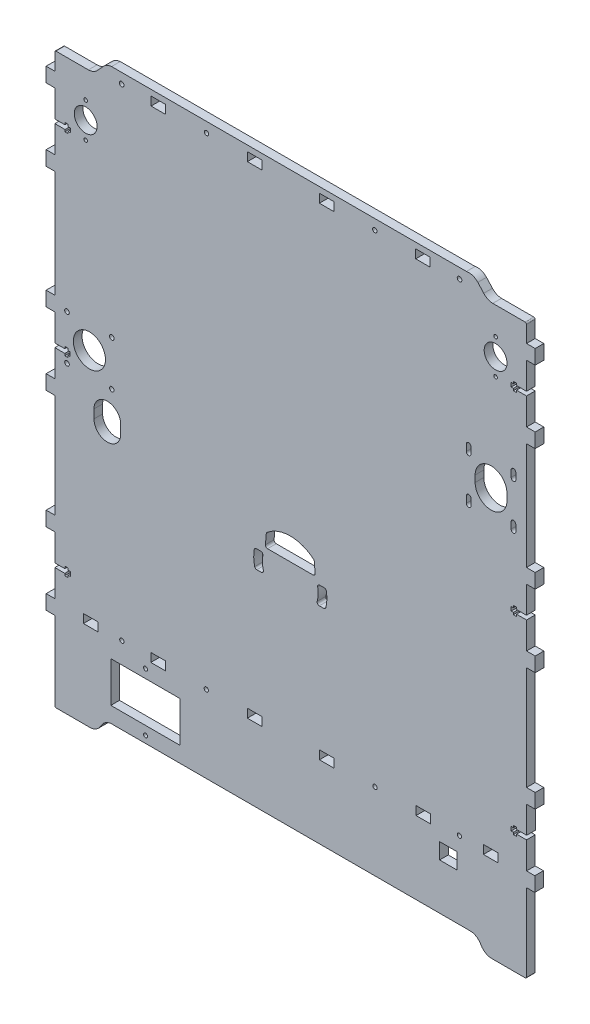
SolidWorks part; units mm, degrees
ref_plane "Спереди" through (0, 0, 0) normal (0, 0, 1) x (1, 0, 0)
ref_plane "Сверху" through (0, 0, 0) normal (0, 1, 0) x (1, 0, 0)
ref_plane "Справа" through (0, 0, 0) normal (1, 0, 0) x (0, 0, -1)
sketch "Эскиз1" plane through (0, 0, 0) normal (0, 0, 1) x (1, 0, 0)
  line L0 (-11.4163, -133.8634) -> (-21.4163, -133.8634)
  line L1 (-21.4163, -133.8634) -> (-21.4163, -127.8634)
  line L2 (-11.4163, -127.8634) -> (-11.4163, -133.8634)
  line L3 (-21.4163, -127.8634) -> (-11.4163, -127.8634)
  line L4 (-61.2563, -127.8634) -> (-61.2563, -133.8634)
  line L5 (-71.2563, -127.8634) -> (-61.2563, -127.8634)
  line L6 (-71.2563, -133.8634) -> (-71.2563, -127.8634)
  line L7 (-61.2563, -133.8634) -> (-71.2563, -133.8634)
  line L8 (61.6637, -152.3271) -> (61.6637, -141.3271)
  line L9 (61.6637, -141.3271) -> (73.7637, -141.3271)
  line L10 (73.7637, -141.3271) -> (73.7637, -152.3271)
  line L11 (73.7637, -152.3271) -> (61.6637, -152.3271)
  line L12 (-197.4876, 21.4243) -> (-197.4866, 20.0542)
  line L13 (-204.4363, 24.2766) -> (-204.4363, 42.8766)
  line L14 (-195.2876, 25.6494) -> (-195.2876, 25.6766)
  line L15 (127.7355, 42.8766) -> (127.7355, 52.8766)
  line L16 (-193.7868, 24.2485) -> (-193.7868, 24.2757)
  line L17 (-195.2868, 24.2757) -> (-195.2876, 25.6494)
  line L18 (-195.2868, 21.4269) -> (-195.2868, 21.4541)
  line L19 (-193.7868, 21.4541) -> (-193.7868, 24.2485)
  line L20 (112.6676, 24.3034) -> (112.6676, 24.2763)
  line L21 (114.8676, 24.3037) -> (114.8674, 25.6766)
  line L22 (-195.2868, 20.0542) -> (-195.2868, 21.4269)
  line L23 (111.1697, 21.5032) -> (111.1697, 21.4761)
  line L24 (111.1676, 24.2752) -> (111.1697, 21.5032)
  line L25 (121.7314, 24.2766) -> (121.7314, 42.8766)
  line L26 (-197.4876, 25.6494) -> (-197.4874, 24.2766)
  line L27 (127.7772, -7.1234) -> (127.7772, 2.8766)
  line L28 (112.6708, 20.1034) -> (112.6708, 20.0763)
  line L29 (-204.4363, 21.4566) -> (-204.4363, 21.4766)
  line L30 (121.7355, 52.8766) -> (121.7355, 127.0366)
  line L31 (-210.4363, 42.8766) -> (-210.4363, 52.8766)
  line L32 (-204.4363, 2.8766) -> (-204.4363, 21.4566)
  line L33 (-204.4363, 52.8766) -> (-204.4363, 127.0366)
  line L34 (-128.0563, -133.8634) -> (-138.0563, -133.8634)
  line L35 (-138.0563, -133.8634) -> (-138.0563, -127.8634)
  line L36 (-138.0563, -127.8634) -> (-128.0563, -127.8634)
  line L37 (-128.0563, -127.8634) -> (-128.0563, -133.8634)
  line L38 (-174.6363, -133.8634) -> (-184.6363, -133.8634)
  line L39 (-184.6363, -133.8634) -> (-184.6363, -127.8634)
  line L40 (-184.6363, -127.8634) -> (-174.6363, -127.8634)
  line L41 (-174.6363, -127.8634) -> (-174.6363, -133.8634)
  line L42 (91.9637, -133.8634) -> (101.9637, -133.8634)
  line L43 (101.9637, -133.8634) -> (101.9637, -127.8634)
  line L44 (101.9637, -127.8634) -> (91.9637, -127.8634)
  line L45 (91.9637, -127.8634) -> (91.9637, -133.8634)
  line L46 (55.3837, -133.8634) -> (45.3837, -133.8634)
  line L47 (45.3837, -133.8634) -> (45.3837, -127.8634)
  line L48 (45.3837, -127.8634) -> (55.3837, -127.8634)
  line L49 (55.3837, -127.8634) -> (55.3837, -133.8634)
  line L50 (-18.1346, -29.194) -> (-21.1843, -29.194)
  line L51 (-21.5365, -41.694) -> (-18.4403, -41.694)
  line L52 (-64.7445, -41.694) -> (-61.6484, -41.694)
  line L53 (-62.0005, -29.194) -> (-65.0502, -29.194)
  line L54 (-58.1883, -16.8245) -> (-58.7957, -23.7669)
  line L55 (-24.3892, -23.7669) -> (-24.9965, -16.8245)
  line L56 (-57.3014, -25.3976) -> (-25.8835, -25.3976)
  line L57 (-165.6924, -145.4128) -> (-165.6924, -173.4128)
  line L58 (-165.6924, -173.4128) -> (-117.6924, -173.4128)
  line L60 (-117.6924, -145.4128) -> (-165.6924, -145.4128)
  line L61 (-181.2137, 199.4366) -> (-203.6703, 199.4366)
  line L62 (-170.8491, 206.6945) -> (-174.9446, 202.2149)
  line L63 (127.478, -128.8434) -> (121.7637, -128.8434)
  line L64 (80.2335, 209.4366) -> (-165.1973, 209.4366)
  line L65 (121.7772, -7.1234) -> (127.7772, -7.1234)
  line L66 (88.0955, 206.8296) -> (92.1957, 202.3542)
  line L67 (98.4674, 199.4366) -> (120.8437, 199.4366)
  line L68 (121.7637, 187.0366) -> (121.7637, 198.5166)
  line L69 (121.7637, 177.0366) -> (127.7637, 177.0366)
  line L70 (127.7637, 177.0366) -> (127.7637, 187.0366)
  line L71 (-204.4363, 42.8766) -> (-210.4363, 42.8766)
  line L72 (120.6695, -193.3271) -> (97.6691, -193.3271)
  line L73 (91.2398, -190.2688) -> (89.1831, -187.2491)
  line L74 (-203.3585, -193.8634) -> (-180.2324, -193.8634)
  line L75 (-210.4363, 177.0366) -> (-210.4363, 187.0366)
  line L76 (114.8517, 158.4366) -> (114.8517, 159.8367)
  line L77 (121.8652, -107.4334) -> (114.8652, -107.4334)
  line L78 (-204.4363, 158.4366) -> (-204.4363, 177.0366)
  line L79 (114.8652, -106.0333) -> (112.6643, -106.0333)
  line L80 (-204.4363, -107.4334) -> (-204.4363, -88.8534)
  line L81 (114.8709, -110.2334) -> (121.7637, -110.2334)
  line L82 (121.8652, -107.4334) -> (121.8652, -88.8534)
  line L83 (111.1668, -110.2331) -> (112.6668, -110.2322)
  line L84 (112.6643, -106.0333) -> (112.6652, -107.4331)
  line L85 (111.1652, -107.434) -> (111.1668, -110.2331)
  line L86 (-197.5237, -111.681) -> (-195.335, -111.6794)
  line L87 (121.7637, 158.4366) -> (114.8517, 158.4366)
  line L88 (114.8708, -111.6332) -> (114.8709, -110.2334)
  line L89 (114.8652, -107.4334) -> (114.8652, -106.0333)
  line L90 (112.6652, -107.4331) -> (111.1652, -107.434)
  line L91 (112.6533, 155.6378) -> (112.6541, 154.2369)
  line L92 (-197.4908, -105.897) -> (-197.4906, -107.4334)
  line L93 (-204.4363, 21.4766) -> (-197.4876, 21.4766)
  line L94 (-197.4876, 21.4766) -> (-197.4876, 21.4243)
  line L95 (-204.4363, 155.6366) -> (-197.3871, 155.6366)
  line L96 (121.7637, -128.8434) -> (121.7637, -110.2334)
  line L97 (121.7801, 2.8766) -> (121.7801, 21.4766)
  line L98 (127.478, -138.8434) -> (127.478, -128.8434)
  line L99 (114.8706, 21.4766) -> (121.7801, 21.4766)
  line L100 (-197.3871, 155.6366) -> (-197.3871, 154.2365)
  line L101 (-197.4181, 158.4366) -> (-204.4363, 158.4366)
  line L102 (-195.2181, 158.419) -> (-195.2181, 159.8366)
  line L103 (112.6668, -110.2322) -> (112.6676, -111.6331)
  line L104 (-197.4906, -107.4334) -> (-204.4363, -107.4334)
  line L105 (112.6508, 159.8367) -> (112.6517, 158.4369)
  line L106 (114.8541, 154.2368) -> (114.8542, 155.6366)
  line L107 (-197.5239, -110.2334) -> (-197.5237, -111.681)
  line L108 (111.1517, 158.436) -> (111.1533, 155.6369)
  line L109 (-195.2876, 25.6766) -> (-197.4876, 25.6766)
  line L110 (112.6708, 20.0763) -> (114.8708, 20.0766)
  line L111 (112.6541, 154.2369) -> (114.8541, 154.2368)
  line L112 (111.1533, 155.6369) -> (112.6533, 155.6378)
  line L113 (121.7772, -78.8534) -> (121.7772, -7.1234)
  line L114 (-195.1863, 155.619) -> (-193.7155, 155.619)
  line L115 (112.6666, 25.6762) -> (112.6676, 24.3034)
  line L116 (114.8676, 24.2766) -> (114.8676, 24.3037)
  line L117 (112.6517, 158.4369) -> (111.1517, 158.436)
  line L118 (-195.3299, -105.8955) -> (-197.4908, -105.897)
  line L119 (-193.6779, -110.2778) -> (-193.6833, -107.2844)
  line L120 (-195.3368, -110.2798) -> (-193.6779, -110.2778)
  line L121 (-197.4866, 20.0542) -> (-195.2868, 20.0542)
  line L122 (-195.2868, 21.4541) -> (-193.7868, 21.4541)
  line L123 (114.8708, 20.0766) -> (114.8708, 20.1037)
  line L124 (-204.4363, -110.2334) -> (-197.5239, -110.2334)
  line L125 (-195.3281, -107.2865) -> (-195.3299, -105.8955)
  line L126 (-193.7868, 24.2757) -> (-195.2868, 24.2757)
  line L127 (-197.3871, 154.2365) -> (-195.1863, 154.2365)
  line L128 (-195.335, -111.6794) -> (-195.3368, -110.2798)
  line L129 (-197.4181, 159.8366) -> (-197.4181, 158.4366)
  line L130 (-193.6833, -107.2844) -> (-195.3281, -107.2865)
  line L131 (-195.1863, 154.2365) -> (-195.1863, 155.619)
  line L133 (114.8517, 159.8367) -> (112.6508, 159.8367)
  line L134 (-193.7155, 155.619) -> (-193.7155, 158.419)
  line L135 (114.8542, 155.6366) -> (121.7637, 155.6366)
  line L136 (-197.4874, 24.2766) -> (-204.4363, 24.2766)
  line L137 (114.8708, 20.1037) -> (114.8706, 21.4766)
  line L138 (-197.4876, 25.6766) -> (-197.4876, 25.6494)
  line L139 (112.6676, -111.6331) -> (114.8708, -111.6332)
  line L140 (112.6676, 24.2763) -> (111.1676, 24.2752)
  line L141 (-195.2181, 159.8366) -> (-197.4181, 159.8366)
  line L142 (121.7637, 158.4366) -> (121.7637, 177.0366)
  line L143 (114.8674, 25.6766) -> (112.6666, 25.6762)
  line L144 (-193.7155, 158.419) -> (-195.2181, 158.419)
  line L145 (-204.4363, -7.1234) -> (-210.4363, -7.1234)
  line L146 (-204.4363, 177.0366) -> (-210.4363, 177.0366)
  line L147 (127.7772, -88.8534) -> (127.7772, -78.8534)
  line L148 (111.1697, 21.4761) -> (112.6697, 21.4772)
  line L149 (121.7314, 24.2766) -> (114.8676, 24.2766)
  line L150 (112.6697, 21.4772) -> (112.6708, 20.1034)
  line L151 (-204.4363, -192.8001) -> (-204.4363, -138.8434)
  line L152 (-204.4363, 137.0366) -> (-204.4363, 155.6366)
  line L153 (-210.4363, 127.0366) -> (-210.4363, 137.0366)
  line L154 (-204.4363, 127.0366) -> (-210.4363, 127.0366)
  line L155 (127.7355, 127.0366) -> (127.7355, 137.0366)
  line L156 (127.7355, 137.0366) -> (121.7637, 137.0366)
  line L157 (-137.8416, 205.4366) -> (-127.8416, 205.4366)
  line L158 (-127.8416, 205.4366) -> (-127.8416, 199.4366)
  line L159 (-127.8416, 199.4366) -> (-137.8416, 199.4366)
  line L160 (-137.8416, 199.4366) -> (-137.8416, 205.4366)
  line L161 (55.1584, 199.4366) -> (45.1584, 199.4366)
  line L162 (45.1584, 199.4366) -> (45.1584, 205.4366)
  line L163 (45.1584, 205.4366) -> (55.1584, 205.4366)
  line L164 (55.1584, 205.4366) -> (55.1584, 199.4366)
  line L165 (-61.2416, 199.4366) -> (-71.2416, 199.4366)
  line L166 (-71.2416, 199.4366) -> (-71.2416, 205.4366)
  line L167 (-71.2416, 205.4366) -> (-61.2416, 205.4366)
  line L169 (-11.4416, 199.4366) -> (-21.4416, 199.4366)
  line L170 (-21.4416, 199.4366) -> (-21.4416, 205.4366)
  line L171 (-21.4416, 205.4366) -> (-11.4416, 205.4366)
  line L173 (127.7637, 187.0366) -> (121.7637, 187.0366)
  line L174 (121.7637, 137.0366) -> (121.7637, 155.6366)
  line L175 (121.7355, 127.0366) -> (127.7355, 127.0366)
  line L176 (-210.4363, 2.8766) -> (-204.4363, 2.8766)
  line L177 (-204.4363, -128.8434) -> (-204.4363, -110.2334)
  line L178 (-204.4363, -78.8534) -> (-204.4363, -7.1234)
  line L179 (-210.4311, -128.8434) -> (-204.4363, -128.8434)
  line L180 (-210.4363, -88.8534) -> (-210.4363, -78.8534)
  line L181 (-210.4363, -7.1234) -> (-210.4363, 2.8766)
  line L182 (-210.4363, -78.8534) -> (-204.4363, -78.8534)
  line L183 (-173.7242, -190.8095) -> (-171.6691, -187.7888)
  line L184 (127.7355, 52.8766) -> (121.7355, 52.8766)
  line L185 (121.7637, -192.6916) -> (121.7637, -138.8434)
  line L186 (-165.2966, -184.2128) -> (82.6717, -184.2128)
  line L187 (-210.4311, -138.8434) -> (-210.4311, -128.8434)
  line L188 (-204.4363, -138.8434) -> (-210.4311, -138.8434)
  line L189 (-210.4363, 137.0366) -> (-204.4363, 137.0366)
  line L190 (-210.4363, 187.0366) -> (-204.4363, 187.0366)
  line L191 (-210.4363, 52.8766) -> (-204.4363, 52.8766)
  line L192 (-204.4363, -88.8534) -> (-210.4363, -88.8534)
  line L193 (121.7637, -138.8434) -> (127.478, -138.8434)
  line L194 (127.7772, -78.8534) -> (121.7772, -78.8534)
  line L195 (127.7772, 2.8766) -> (121.7801, 2.8766)
  line L196 (-204.4363, 187.0366) -> (-204.4363, 198.2588)
  line L197 (121.7314, 42.8766) -> (127.7355, 42.8766)
  line L198 (121.8652, -88.8534) -> (127.7772, -88.8534)
  line L199 (-158.8564, -7.694) -> (-158.8564, -1.694)
  line L200 (86.2572, 90.556) -> (86.2572, 86.056)
  line L201 (111.1572, 75.056) -> (111.1572, 70.556)
  line L202 (108.2572, 86.056) -> (108.2572, 90.556)
  line L203 (114.3572, 101.556) -> (114.3572, 106.056)
  line L204 (111.1572, 106.056) -> (111.1572, 101.556)
  line L205 (114.3572, 70.556) -> (114.3572, 75.056)
  line L206 (80.1572, 75.056) -> (80.1572, 70.556)
  line L207 (83.3572, 70.556) -> (83.3572, 75.056)
  line L208 (83.3572, 101.556) -> (83.3572, 106.056)
  line L209 (-177.3564, -1.694) -> (-177.3564, -7.694)
  line L210 (80.1572, 106.056) -> (80.1572, 101.556)
  line L211 (-61.2416, 205.4366) -> (-61.2416, 199.4366)
  line L212 (-11.4416, 199.4366) -> (-11.4416, 205.4366)
  line L213 (-141.6924, -188.6041) -> (-141.6924, -132.5824) construction
  line L214 (-195.203, -133.8634) -> (114.843, -133.8634) construction
  line L215 (-204.4363, 213.0066) -> (-204.4363, -217.9418) construction
  line L216 (121.7637, 210.9354) -> (121.7637, -201.1521) construction
  line L217 (100.4084, 185.062) -> (100.4084, 147.8448) construction
  line L218 (-183.0863, 187.5106) -> (-183.0863, 152.6137) construction
  line L219 (-117.6924, -145.4128) -> (-117.6924, -173.4128)
  arc A0 (80.1572, 70.556) -> (83.3572, 70.556) centre (81.7572, 70.556) ccw
  arc A1 (80.1572, 101.556) -> (83.3572, 101.556) centre (81.7572, 101.556) ccw
  circle A2 centre (-183.0863, 168.4366) radius 7.9
  circle A3 centre (100.4084, 168.4366) radius 7.9
  arc A4 (-16.6559, -30.4419) -> (-18.1346, -29.194) centre (-18.1346, -30.694) ccw
  arc A5 (-21.1843, -29.194) -> (-22.6563, -30.9825) centre (-21.1843, -30.694) ccw
  arc A6 (-22.9831, -39.7973) -> (-22.6563, -30.9825) centre (-41.5924, -34.694) ccw
  arc A7 (-22.9831, -39.7973) -> (-21.5365, -41.694) centre (-21.5365, -40.194) ccw
  arc A8 (-65.0502, -29.194) -> (-66.5289, -30.4419) centre (-65.0502, -30.694) ccw
  arc A9 (-66.5289, -30.4419) -> (-66.2039, -40.5407) centre (-41.5924, -34.694) ccw
  arc A10 (-66.2039, -40.5407) -> (-64.7445, -41.694) centre (-64.7445, -40.194) ccw
  arc A11 (-61.6484, -41.694) -> (-60.2018, -39.7973) centre (-61.6484, -40.194) ccw
  arc A12 (-60.5285, -30.9825) -> (-60.2018, -39.7973) centre (-41.5924, -34.694) ccw
  arc A13 (-60.5285, -30.9825) -> (-62.0005, -29.194) centre (-62.0005, -30.694) ccw
  arc A14 (-16.9809, -40.5407) -> (-16.6559, -30.4419) centre (-41.5924, -34.694) ccw
  arc A15 (-18.4403, -41.694) -> (-16.9809, -40.5407) centre (-18.4403, -40.194) ccw
  arc A16 (-57.6664, -15.8131) -> (-58.1883, -16.8245) centre (-56.694, -16.9552) ccw
  arc A17 (-25.5185, -15.8131) -> (-57.6664, -15.8131) centre (-41.5924, -34.694) ccw
  arc A18 (-24.9965, -16.8245) -> (-25.5185, -15.8131) centre (-26.4908, -16.9552) ccw
  arc A19 (-25.8835, -25.3976) -> (-24.3892, -23.7669) centre (-25.8835, -23.8976) ccw
  arc A20 (-58.7957, -23.7669) -> (-57.3014, -25.3976) centre (-57.3014, -23.8976) ccw
  circle A21 centre (-158.1416, 202.4366) radius 1.6
  arc A22 (-203.6703, 199.4366) -> (-204.4363, 198.2588) centre (-203.5603, 198.5271) ccw
  arc A23 (-181.2137, 199.4366) -> (-174.9446, 202.2149) centre (-181.2321, 207.9403) ccw
  arc A24 (-165.1973, 209.4366) -> (-170.8491, 206.6945) centre (-164.5754, 200.9594) ccw
  circle A25 centre (75.4584, 202.4366) radius 1.6
  arc A26 (88.0955, 206.8296) -> (80.2335, 209.4366) centre (81.8282, 201.0876) ccw
  arc A27 (-180.2324, -193.8634) -> (-173.7242, -190.8095) centre (-180.2521, -185.3595) ccw
  arc A28 (120.6695, -193.3271) -> (121.7637, -192.6916) centre (120.7618, -192.2263) ccw
  arc A29 (-165.2966, -184.2128) -> (-171.6691, -187.7888) centre (-164.7271, -192.6937) ccw
  arc A30 (-204.4363, -192.8001) -> (-203.3585, -193.8634) centre (-203.4855, -192.9141) ccw
  arc A31 (89.1831, -187.2491) -> (82.6717, -184.2128) centre (82.6717, -192.7128) ccw
  arc A32 (91.2398, -190.2688) -> (97.6691, -193.3271) centre (97.7466, -184.877) ccw
  arc A34 (92.1957, 202.3542) -> (98.4674, 199.4366) centre (98.6272, 207.9796) ccw
  circle A35 centre (16.8584, 202.4366) radius 1.5
  circle A36 centre (-99.5416, 202.4366) radius 1.5
  circle A37 centre (-196.0064, 47.306) radius 1.6
  arc A38 (-177.3564, -7.694) -> (-158.8564, -7.694) centre (-168.1064, -7.694) ccw
  circle A39 centre (-165.0064, 16.306) radius 1.6
  circle A40 centre (-196.0064, 16.306) radius 1.6
  arc A41 (86.2572, 86.056) -> (108.2572, 86.056) centre (97.2572, 86.056) ccw
  arc A42 (108.2572, 90.556) -> (86.2572, 90.556) centre (97.2572, 90.556) ccw
  arc A43 (114.3572, 75.056) -> (111.1572, 75.056) centre (112.7572, 75.056) ccw
  circle A44 centre (-180.5064, 31.806) radius 11.1
  circle A45 centre (-165.0064, 47.306) radius 1.6
  arc A46 (114.3572, 106.056) -> (111.1572, 106.056) centre (112.7572, 106.056) ccw
  arc A47 (111.1572, 101.556) -> (114.3572, 101.556) centre (112.7572, 101.556) ccw
  arc A48 (111.1572, 70.556) -> (114.3572, 70.556) centre (112.7572, 70.556) ccw
  arc A49 (83.3572, 75.056) -> (80.1572, 75.056) centre (81.7572, 75.056) ccw
  arc A50 (-158.8564, -1.694) -> (-177.3564, -1.694) centre (-168.1064, -1.694) ccw
  arc A51 (83.3572, 106.056) -> (80.1572, 106.056) centre (81.7572, 106.056) ccw
  circle A52 centre (75.3837, -130.8634) radius 1.5
  circle A53 centre (16.9837, -130.8634) radius 1.5
  circle A54 centre (-99.6563, -130.8634) radius 1.5
  circle A55 centre (-158.0563, -130.8634) radius 1.5
  arc A57 (121.7637, 198.5166) -> (120.8437, 199.4366) centre (120.8437, 198.5166) ccw
  circle A58 centre (-141.6924, -179.4128) radius 1.4
  circle A59 centre (-141.6924, -139.4128) radius 1.4
  circle A60 centre (100.4084, 180.4366) radius 1.25
  circle A61 centre (100.4084, 156.4366) radius 1.25
  circle A62 centre (-183.0863, 180.4366) radius 1.25
  circle A63 centre (-183.0863, 156.4366) radius 1.25
  point P319 (-207.4363, 187.0366)
  point P322 (-11.4416, 202.4366)
  point P330 (-21.4163, -130.8634)
  point P331 (55.3837, -130.8634)
  dimension "D1" = 15.8
  dimension "D2" = 15.8
  dimension "D3" = 22.2
  dimension "D6" = 19.8
  dimension "D35" = 12.1
  dimension "D38" = 48
  dimension "D43" = 12
  dimension "D96" = 2.8
  dimension "D97" = 2.8
  dimension "D40" = 2.5
  dimension "D42" = 2.5
  dimension "D44" = 12
  dimension "D46" = 2.5
  dimension "D49" = 2.5
  dimension "D51" = 12
  dimension "D52" = 12
  dimension "D56" = 6
  dimension "D59" = 6
  dimension "D60" = 24
  dimension "D4" = 403.3
  dimension "D7" = 326.2
  dimension "D10" = 12.4
  dimension "D11" = 10
  dimension "D13" = 6
  dimension "D14" = 19.8
  dimension "D15" = 4
  dimension "D16" = 7
  dimension "D17" = 7
  dimension "D18" = 4
  dimension "D19" = 4
  dimension "D20" = 7
  dimension "D21" = 7
  dimension "D22" = 4
  dimension "D23" = 6
  dimension "D24" = 28.3
  dimension "D25" = 28.3
  dimension "D26" = 28.3
  dimension "D27" = 39.84
  dimension "D28" = 10
  dimension "D29" = 10
  dimension "D30" = 10
  dimension "D31" = 10
  dimension "D32" = 11
  dimension "D33" = 21.35
  dimension "D34" = 41
  dimension "D36" = 6
  dimension "D37" = 6
  dimension "D39" = 28.3
  dimension "D41" = 31
  dimension "D45" = 18.6
  dimension "D47" = 2.8
  dimension "D48" = 18.6
  dimension "D50" = 10
  dimension "D53" = 48
  dimension "D54" = 48
  dimension "D55" = 28
  dimension "D57" = 31
  dimension "D58" = 31
  dimension "D61" = 24
  dimension "D83" = 71.73
  dimension "D84" = 10
  dimension "D85" = 6
  dimension "D88" = 6
  dimension "D89" = 18.58
  dimension "D90" = 2.8
  dimension "D98" = 4.8
  dimension "D99" = 44.8
  dimension "D100" = 60
  dimension "D101" = 6
  dimension "D102" = 10
  dimension "D103" = 3
  dimension "D104" = 6
  dimension "D105" = 10
  dimension "D106" = 3
  dimension "D107" = 6
  dimension "D108" = 10
  dimension "D109" = 6
  dimension "D110" = 10
  dimension "D111" = 3
  dimension "D112" = 6
  dimension "D113" = 10
  dimension "D114" = 3
  dimension "D115" = 6
  dimension "D116" = 10
  dimension "D118" = 16.58
  dimension "D119" = 20
  dimension "D120" = 28.4
  dimension "D121" = 28.4
  dimension "D123" = 16.58
  dimension "D124" = 20
  dimension "D125" = 28.4
  dimension "D126" = 28.4
extrude "Бобышка-Вытянуть1" add sketch "Эскиз1" along normal blind 6
